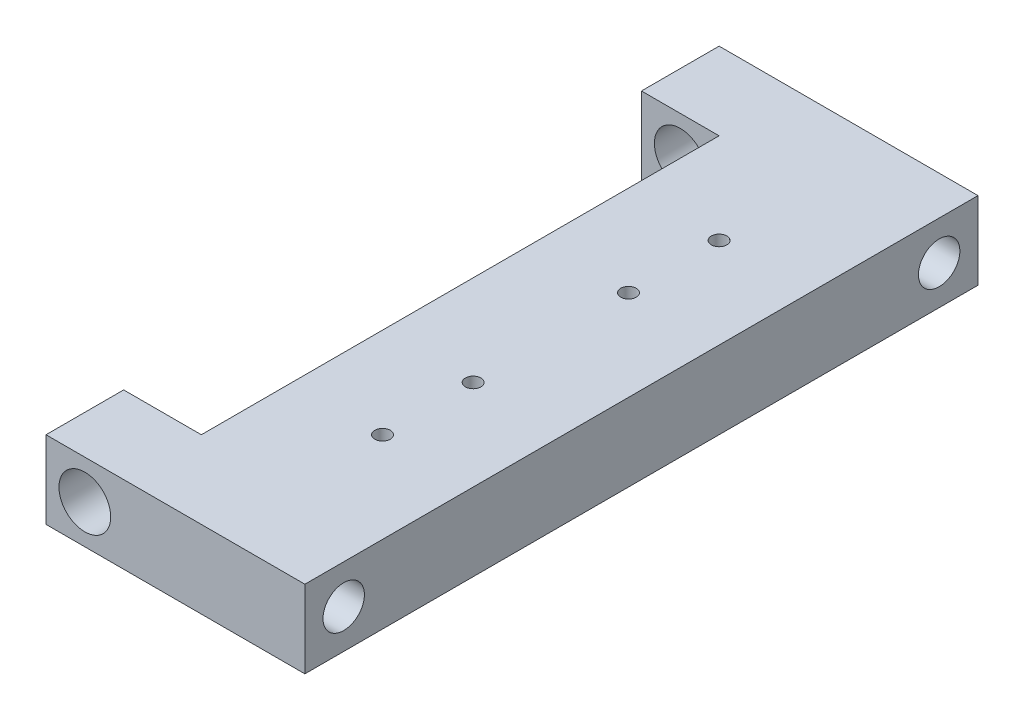
SolidWorks part; units mm, degrees
ref_plane "Plan de face" through (0, 0, 0) normal (0, 0, 1) x (1, 0, 0)
ref_plane "Plan de dessus" through (0, 0, 0) normal (0, 1, 0) x (1, 0, 0)
ref_plane "Plan de droite" through (0, 0, 0) normal (1, 0, 0) x (0, 0, -1)
sketch "Esquisse1" plane through (0, 0, 0) normal (0, 0, 1) x (1, 0, 0)
  line L0 (11.1498, 0) -> (0, 0) construction
  line L1 (0, 0) -> (0, 15.3125) construction
  line L3 (-7.5, 7.5) -> (7.5, 7.5)
  line L4 (-7.5, 7.5) -> (-7.5, -7.5)
  line L5 (-7.5, -7.5) -> (7.5, -7.5)
  line L6 (7.5, 7.5) -> (7.5, -7.5)
  line L7 (7.5, 7.5) -> (42.5, 7.5)
  line L8 (7.5, 7.5) -> (7.5, -7.5)
  line L9 (7.5, -7.5) -> (42.5, -7.5)
  line L10 (42.5, 7.5) -> (42.5, -7.5)
  circle A0 centre (0, 0) radius 5
  dimension "D1" = 10
  dimension "D2" = 15
  dimension "D3" = 15
  dimension "D4" = 35
extrude "Boss.-Extru.1" add sketch "Esquisse1" along normal blind 130 contours L6 L3 L4 L5 A0 | L10 L7 L6 L9
sketch "Esquisse2" plane through (0, 7.5, 0) normal (0, 1, 0) x (1, 0, 0)
  line L0 (-7.5, -130) -> (-7.5, 0) construction
  line L1 (-7.5, -15) -> (7.5, -15)
  line L2 (-7.5, -15) -> (-7.5, -115)
  line L3 (-7.5, -115) -> (7.5, -115)
  line L4 (7.5, -15) -> (7.5, -115)
  line L5 (-7.5, 0) -> (42.5, 0) construction
  line L6 (-7.5, -130) -> (42.5, -130) construction
  dimension "D1" = 15
  dimension "D2" = 15
  dimension "D3" = 15
extrude "Enlèv. mat.-Extru.1" cut sketch "Esquisse2" against normal blind 60
sketch "Esquisse3" plane through (42.5, 0, 0) normal (1, 0, 0) x (0, 0, -1)
  line L0 (-130, 0) -> (0, 0) construction
  line L1 (-130, 7.5) -> (-130, -7.5) construction
  line L2 (0, 0) -> (-65, 7.5) construction
  line L3 (-130, 7.5) -> (0, 7.5) construction
  line L4 (-65, 7.5) -> (-65, -7.5) construction
  line L5 (-130, -7.5) -> (0, -7.5) construction
  circle A0 centre (-122.5, 0) radius 4
  circle A1 centre (-7.5, 0) radius 4
  dimension "D1" = 8
  dimension "D2" = 7.5
extrude "Enlèv. mat.-Extru.2" cut sketch "Esquisse3" against normal blind 35
sketch "Esquisse4" plane through (0, 7.5, 0) normal (0, 1, 0) x (1, 0, 0)
  line L0 (42.5, -65) -> (7.5, -65) construction
  line L1 (42.5, -130) -> (42.5, 0) construction
  line L2 (7.5, -115) -> (7.5, -15) construction
  line L3 (25, -65) -> (25, 0) construction
  line L4 (-7.5, 0) -> (42.5, 0) construction
  circle A0 centre (25, -32.5) radius 1.5
  circle A1 centre (25, -97.5) radius 1.5
  dimension "D2" = 3
extrude "Enlèv. mat.-Extru.3" cut sketch "Esquisse4" against normal blind 5
sketch "Esquisse5" plane through (0, 7.5, 0) normal (0, 1, 0) x (1, 0, 0)
  line L0 (7.5, -65) -> (42.5, -65) construction
  line L1 (7.5, -115) -> (7.5, -15) construction
  line L2 (42.5, -130) -> (42.5, 0) construction
  circle A0 centre (25, -50) radius 1.5
  circle A1 centre (25, -80) radius 1.5
  dimension "D1" = 3
  dimension "D2" = 15
  dimension "D3" = 17.5
extrude "Enlèv. mat.-Extru.4" cut sketch "Esquisse5" against normal blind 15
